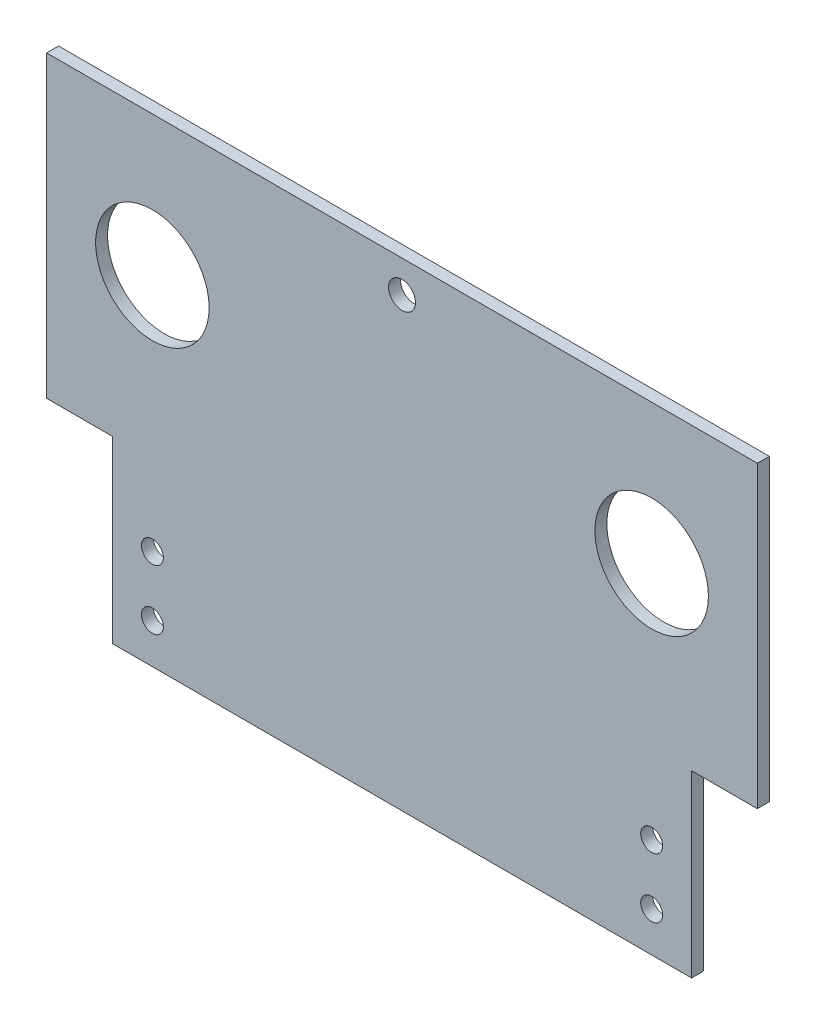
SolidWorks part; units mm, degrees
ref_plane "Front Plane" through (0, 0, 0) normal (0, 0, 1) x (1, 0, 0)
ref_plane "Top Plane" through (0, 0, 0) normal (0, 1, 0) x (1, 0, 0)
ref_plane "Right Plane" through (0, 0, 0) normal (1, 0, 0) x (0, 0, -1)
sketch "Sketch1" plane through (0, 0, 0) normal (0, 0, 1) x (1, 0, 0)
  line L1 (0, 0) -> (178.16, 0)
  line L2 (0, 0) -> (0, -120)
  line L3 (0, -120) -> (178.16, -120)
  line L4 (178.16, 0) -> (178.16, -120)
  dimension "D1" = 120
  dimension "D2" = 178.16
extrude "Boss-Extrude1" add sketch "Sketch1" along normal blind 3
sketch "Sketch2" plane through (0, 0, 3) normal (0, 0, 1) x (1, 0, 0)
  line L0 (0, 0) -> (0, -120) construction
  line L1 (178.16, -120) -> (178.16, 0) construction
  line L2 (0, -120) -> (178.16, -120) construction
  line L3 (178.16, 0) -> (0, 0) construction
  circle A0 centre (26.5, -35) radius 14.225
  circle A1 centre (151.66, -35) radius 14.225
  circle A3 centre (26.5, -110) radius 2.75
  circle A4 centre (151.66, -110) radius 2.75
  circle A7 centre (89.08, -8) radius 3.375
  circle A8 centre (26.5, -95) radius 2.75
  circle A9 centre (151.66, -95) radius 2.75
  point P11 (89.08, 0)
  dimension "D1" = 28.45
  dimension "D2" = 28.45
  dimension "D3" = 10
  dimension "D4" = 5.5
  dimension "D5" = 6.75
  dimension "D7" = 5.5
  dimension "D14" = 5.5
  dimension "D17" = 5.5
  dimension "D9" = 26.5
  dimension "D10" = 26.5
  dimension "D12" = 35
  dimension "D13" = 8
  dimension "D15" = 15
  dimension "D16" = 15
extrude "Cut-Extrude1" cut sketch "Sketch2" against normal through all
sketch "Sketch3" plane through (0, 0, 0) normal (0, 0, -1) x (-1, 0, 0)
  line L1 (0, -120) -> (-16.5, -120)
  line L2 (0, -120) -> (0, -75)
  line L3 (0, -75) -> (-16.5, -75)
  line L4 (-16.5, -120) -> (-16.5, -75)
  line L5 (-178.16, -120) -> (-161.66, -120)
  line L6 (-178.16, -120) -> (-178.16, -75)
  line L7 (-178.16, -75) -> (-161.66, -75)
  line L8 (-161.66, -120) -> (-161.66, -75)
  dimension "D1" = 16.5
  dimension "D2" = 45
  dimension "D3" = 16.5
  dimension "D4" = 45
extrude "Cut-Extrude2" cut sketch "Sketch3" against normal through all
